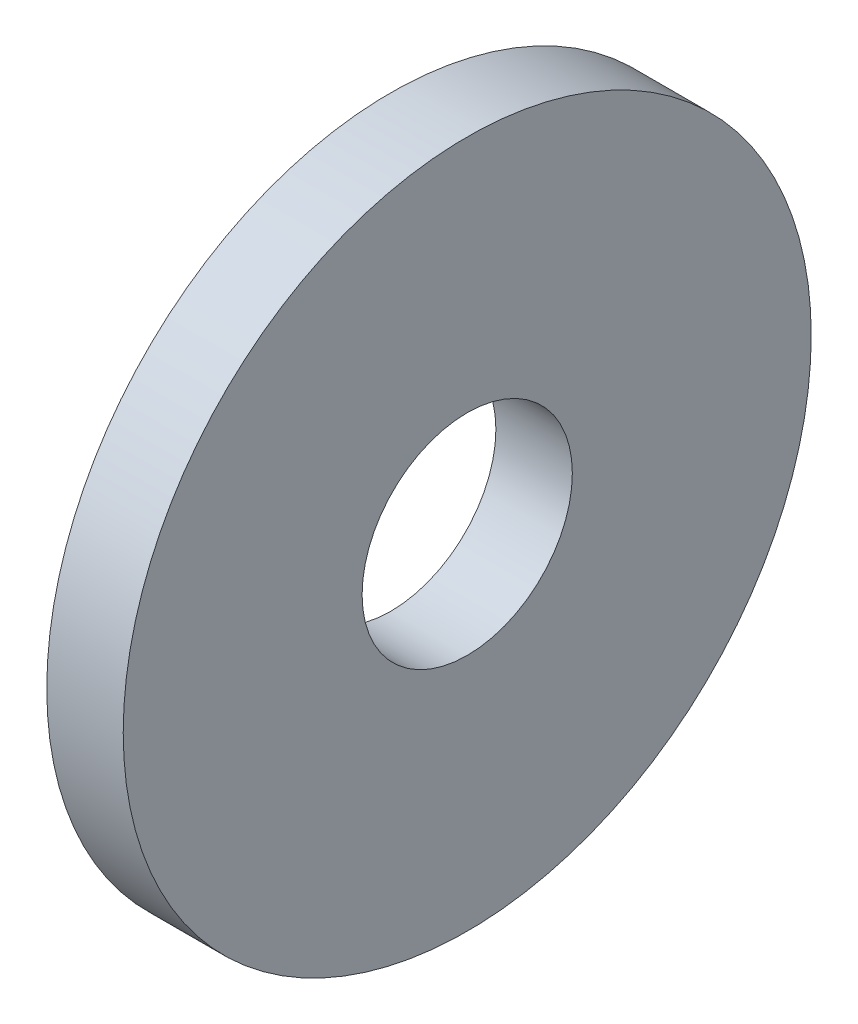
SolidWorks part; units mm, degrees
ref_plane "Plane1" through (0, 0, 0) normal (0, 0, 1) x (1, 0, 0)
ref_plane "Plane2" through (0, 0, 0) normal (0, 1, 0) x (1, 0, 0)
ref_plane "Plane3" through (0, 0, 0) normal (1, 0, 0) x (0, 0, -1)
sketch "Sketch1" plane through (0, 0, 0) normal (0, 0, 1) x (1, 0, 0)
  line L0 (-34.925, 0) -> (9.525, 0) construction
  line L1 (0, 2.75) -> (0, 9)
  line L2 (0, 9) -> (-2, 9)
  line L3 (-2, 9) -> (-2, 2.75)
  line L4 (-2, 2.75) -> (0, 2.75)
  dimension "Thickness" = 2
  dimension "Inside_dia" = 5.5
  dimension "Outside_dia" = 18
revolve "Base-Revolve" add sketch "Sketch1" angle 360 about L0
